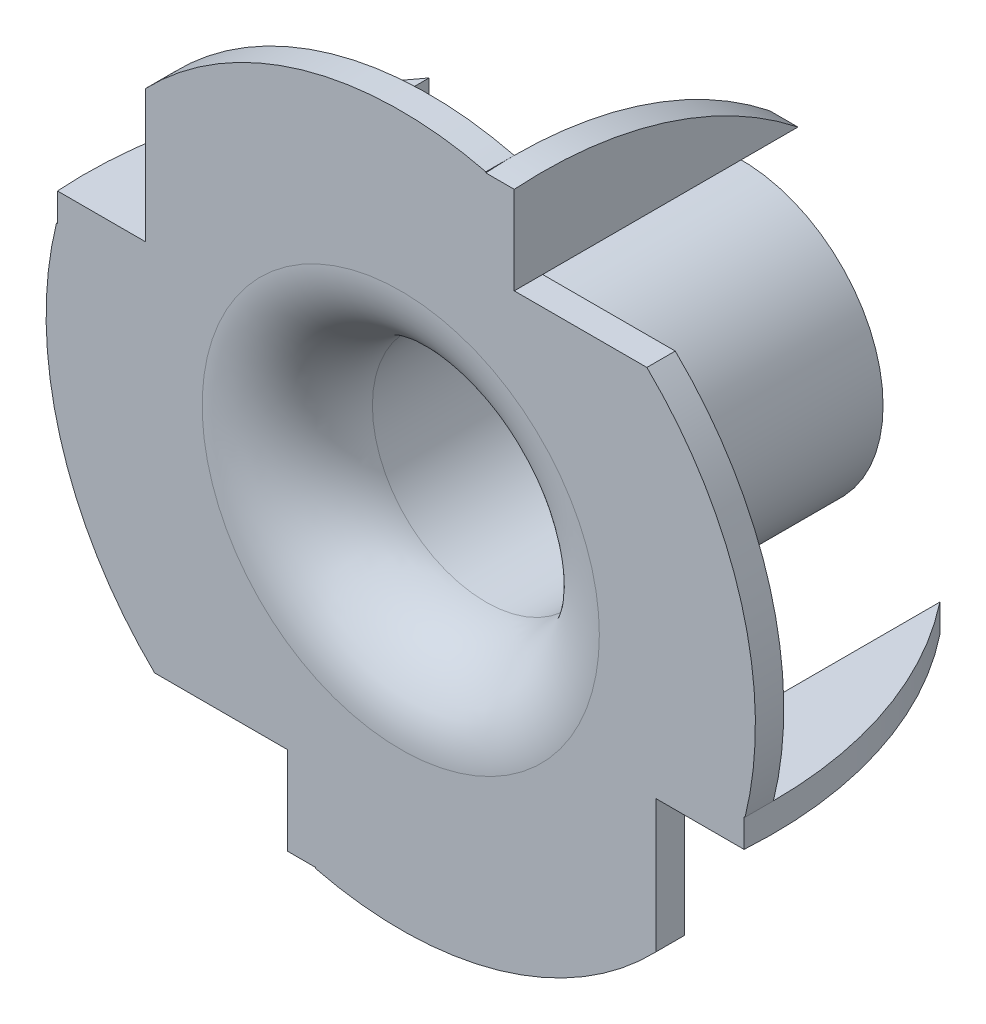
SolidWorks part; units mm, degrees
ref_plane "Front Plane" through (0, 0, 0) normal (0, 0, 1) x (1, 0, 0)
ref_plane "Top Plane" through (0, 0, 0) normal (0, 1, 0) x (1, 0, 0)
ref_plane "Right Plane" through (0, 0, 0) normal (1, 0, 0) x (0, 0, -1)
sketch "Sketch1" plane through (0, 0, 0) normal (0, 1, 0) x (1, 0, 0)
  line L5 (0, 0) -> (7.1583, 0) construction
  line L6 (12.5, 0) -> (12.5, 11.5) construction
  line L7 (8.5, 7.0328) -> (8.5, 2.5)
  line L8 (8, 2.5) -> (8, 11.5) construction
  line L10 (0, -0.5) -> (5.5, -0.5)
  line L11 (8.5, 7.0328) -> (8.5, 11.5)
  line L14 (0, 0.5) -> (5.5, 0.5)
  line L15 (7.5, 2.5) -> (7.5, 11.5)
  line L18 (0, -0.5) -> (0, 0.5)
  line L19 (8.5, 11.5) -> (7.5, 11.5)
  line L24 (8.5, -0.5) -> (8.5, 11.5) construction
  line L25 (8, 0) -> (8, 11.5) construction
  line L26 (0, 0) -> (8, 0) construction
  line L27 (0, -0.5) -> (8.5, -0.5) construction
  line L28 (0, 0.5) -> (7.5, 0.5) construction
  line L29 (7.5, 0.5) -> (7.5, 11.5) construction
  arc A0 (5.5, -0.5) -> (8.5, 2.5) centre (5.5, 2.5) ccw
  arc A1 (5.5, 0.5) -> (7.5, 2.5) centre (5.5, 2.5) ccw
  dimension "D7" = 6
  dimension "D1" = 12.5
  dimension "D2" = 12
  dimension "D6" = 4
  dimension "D5" = 0.5
  dimension "D8" = 1
revolve "Revolve1" add sketch "Sketch1" angle 360 about L6
sketch "Sketch2" plane through (0, 0, -0.5) normal (0, 0, -1) x (-1, 0, 0)
  line L0 (-12.5, 0) -> (-12.5, 12.5) construction
  line L1 (-12.5, 12.5) -> (-12.5, 0) construction
  line L2 (-12.5, 0) -> (0, 0) construction
  line L3 (-3.5, 8.6747) -> (-3.5, 3)
  line L4 (-3.5, 3) -> (-0.3653, 3)
  line L5 (-3.8253, -9) -> (-9.5, -9)
  line L6 (-9.5, -9) -> (-9.5, -12.1347)
  line L7 (-21.5, -8.6747) -> (-21.5, -3)
  line L8 (-21.5, -3) -> (-24.6347, -3)
  line L9 (-21.1747, 9) -> (-15.5, 9)
  line L10 (-15.5, 9) -> (-15.5, 12.1347)
  circle A0 centre (-12.5, 0) radius 12.5 construction
  arc A1 (-9.5, -12.1347) -> (-3.8253, -9) centre (-12.5, 0) ccw
  circle A2 centre (-12.5, 0) radius 12.5
  arc A3 (-0.3653, 3) -> (-3.5, 8.6747) centre (-12.5, 0) ccw
  arc A4 (-24.6347, -3) -> (-21.5, -8.6747) centre (-12.5, 0) ccw
  arc A5 (-15.5, 12.1347) -> (-21.1747, 9) centre (-12.5, 0) ccw
  point P24 (-12.5, 0)
  dimension "D1" = 3
  dimension "D2" = 9
  dimension "D3" = 0
  dimension "D4" = 4
extrude "Cut-Extrude1" cut sketch "Sketch2" against normal through all both and the other way through all
sketch "Sketch3" plane through (0, 3, 0) normal (0, 1, 0) x (1, 0, 0)
  line L0 (3.5, 0.5) -> (3.5, 9.5)
  line L4 (3.5, 0.5) -> (0.3653, 0.5)
  line L5 (0.3653, 0.5) -> (0.3653, -0.5)
  line L6 (0.3653, -0.5) -> (3.5, -0.5)
  line L7 (3.5, -0.5) -> (3.5, 0.5)
  line L9 (0.3653, 0.5) -> (0.3653, -0.5)
  line L10 (0.3653, -0.5) -> (3.5, -0.5)
  line L11 (3.5, -0.5) -> (3.5, 0.5)
  arc A0 (3.5, 9.5) -> (0.3999, -0.5) centre (14.8527, 0.5) ccw
  point P7 (10.6841, 1.9519)
  line M6 (3.5, 0.5) -> (0.3653, 0.5)
  line M9 (3.5, -0.5) -> (3.5, 0.5)
  dimension "D2" = 9
  dimension "D1" = 0
extrude "Boss-Extrude1" add sketch "Sketch3" along normal blind 1 contours L0 A0 M6 | A0 L10 M6 M9
pattern_circular "CirPattern4" count 4 over 360 about axis through (12.5, 0, 0) along (0, 0, 1) of "Boss-Extrude1"
